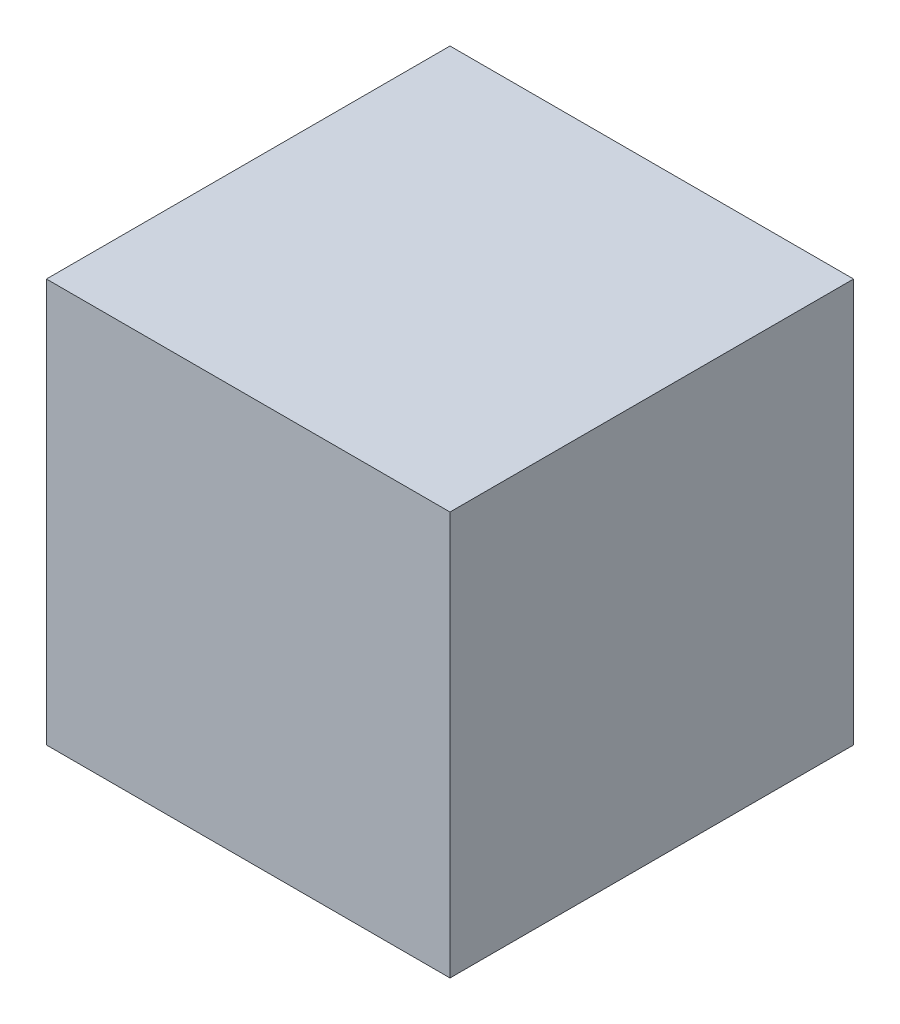
SolidWorks part; units mm, degrees
ref_plane "Front Plane" through (0, 0, 0) normal (0, 0, 1) x (1, 0, 0)
ref_plane "Top Plane" through (0, 0, 0) normal (0, 1, 0) x (1, 0, 0)
ref_plane "Right Plane" through (0, 0, 0) normal (1, 0, 0) x (0, 0, -1)
sketch "Sketch1" plane through (0, 0, 0) normal (0, 1, 0) x (1, 0, 0)
  line L1 (-43.7767, 1172.4951) -> (1175.4233, 1172.4951)
  line L2 (-43.7767, 1172.4951) -> (-43.7767, -46.7049)
  line L3 (-43.7767, -46.7049) -> (1175.4233, -46.7049)
  line L4 (1175.4233, 1172.4951) -> (1175.4233, -46.7049)
  dimension "D1" = 1219.2
  dimension "D2" = 1219.2
extrude "Boss-Extrude1" add sketch "Sketch1" along normal blind 1219.2
